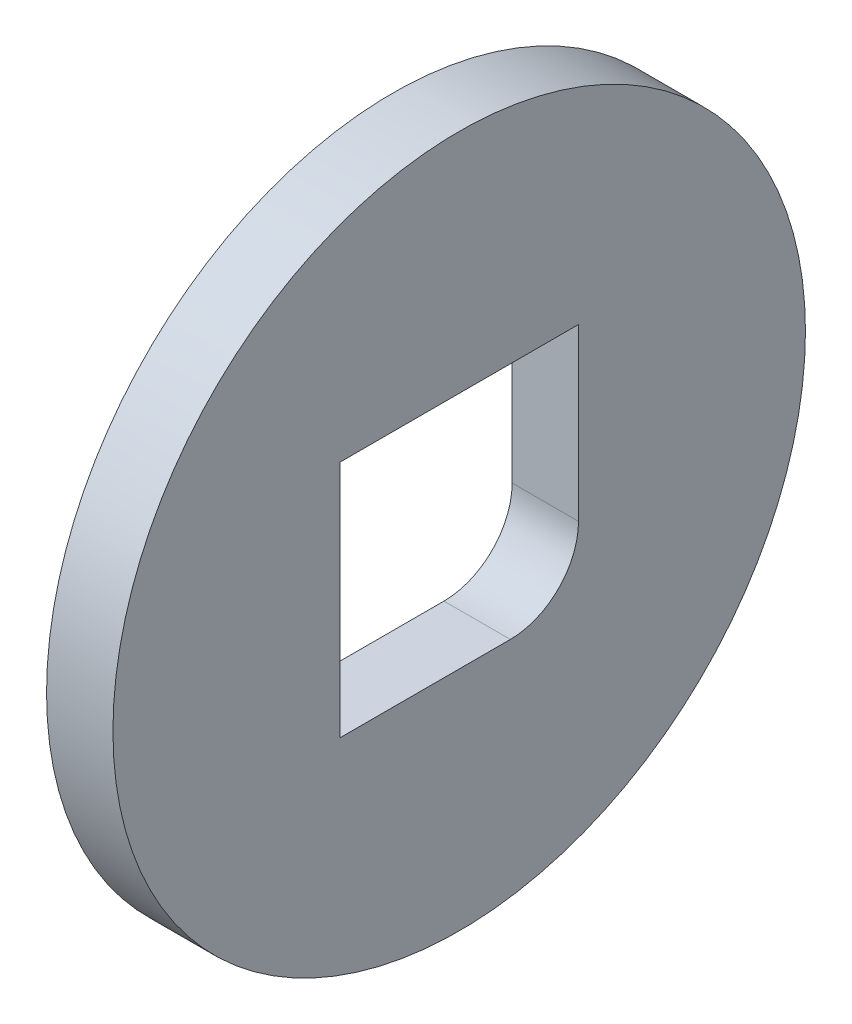
SolidWorks part; units mm, degrees
ref_plane "Plan de face" through (0, 0, 0) normal (0, 0, 1) x (1, 0, 0)
ref_plane "Plan de dessus" through (0, 0, 0) normal (0, 1, 0) x (1, 0, 0)
ref_plane "Plan de droite" through (0, 0, 0) normal (1, 0, 0) x (0, 0, -1)
sketch "Esquisse1" plane through (0, 0, 0) normal (0, 0, 1) x (1, 0, 0)
  line L0 (0, 0) -> (0, 50.7779)
  line L1 (0, 50.7779) -> (9.7341, 50.7779)
  line L2 (9.7341, 50.7779) -> (9.7341, 0)
  line L3 (9.7341, 0) -> (0, 0)
revolve "Révolution1" add sketch "Esquisse1" angle 360 about L3
sketch "Esquisse2" plane through (9.7341, 0, 0) normal (1, 0, 0) x (0, 0, -1)
  line L1 (17.5, 17.5) -> (-17.5, 17.5)
  line L2 (17.5, 17.5) -> (17.5, -17.5)
  line L3 (17.5, -17.5) -> (-17.5, -17.5)
  line L4 (-17.5, 17.5) -> (-17.5, -17.5)
  line L5 (17.5, 17.5) -> (-17.5, -17.5) construction
  line L6 (17.5, -17.5) -> (-17.5, 17.5) construction
  point P0 (0, 0)
  dimension "D1" = 35
  dimension "D2" = 35
extrude "Enlèv. mat.-Extru.1" cut sketch "Esquisse2" against normal through all
fillet "Congé2" radius 10 1 edges at (4.867, -17.5, -17.5)
